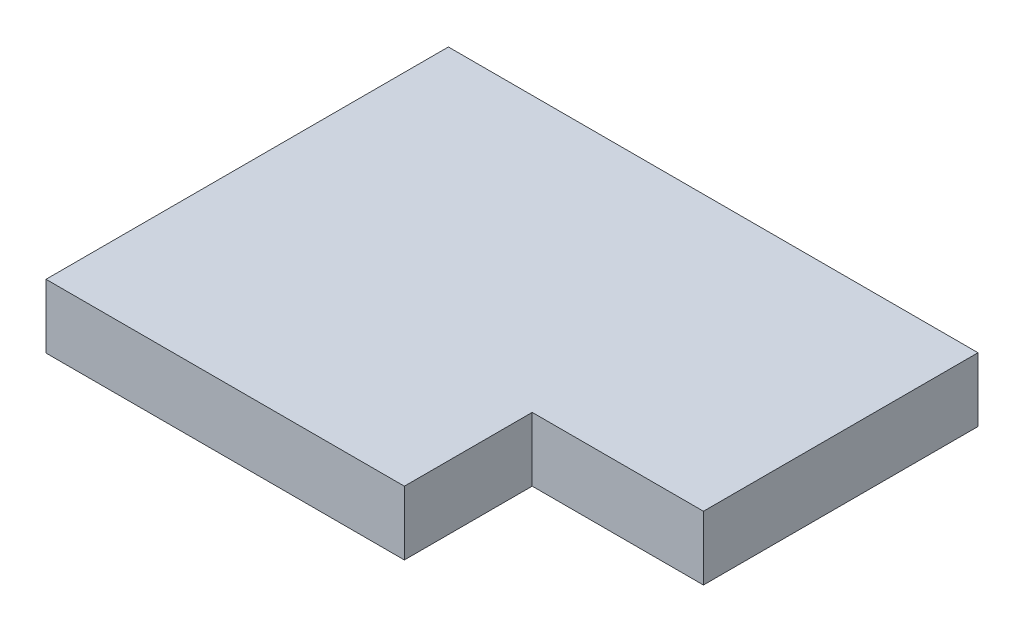
SolidWorks part; units mm, degrees
ref_plane "Front Plane" through (0, 0, 0) normal (0, 0, 1) x (1, 0, 0)
ref_plane "Top Plane" through (0, 0, 0) normal (0, 1, 0) x (1, 0, 0)
ref_plane "Right Plane" through (0, 0, 0) normal (1, 0, 0) x (0, 0, -1)
sketch "Sketch1" plane through (0, 0, 0) normal (0, 1, 0) x (1, 0, 0)
  line L1 (-435, 330.5) -> (435, 330.5)
  line L2 (-435, 330.5) -> (-435, -330.5)
  line L3 (-435, -330.5) -> (435, -330.5)
  line L4 (435, 330.5) -> (435, -330.5)
  line L5 (-435, 330.5) -> (435, -330.5) construction
  line L6 (-435, -330.5) -> (435, 330.5) construction
  point P0 (0, 0)
  dimension "D1" = 870
  dimension "D2" = 661
extrude "Boss-Extrude1" add sketch "Sketch1" along normal blind 105
sketch "Sketch2" plane through (0, 105, 0) normal (0, 1, 0) x (1, 0, 0)
  line L1 (435, -330.5) -> (153.7, -330.5)
  line L2 (435, -330.5) -> (435, -120.5)
  line L3 (435, -120.5) -> (153.7, -120.5)
  line L4 (153.7, -330.5) -> (153.7, -120.5)
  dimension "D1" = 281.3
  dimension "D2" = 210
extrude "Cut-Extrude1" cut sketch "Sketch2" against normal through all
